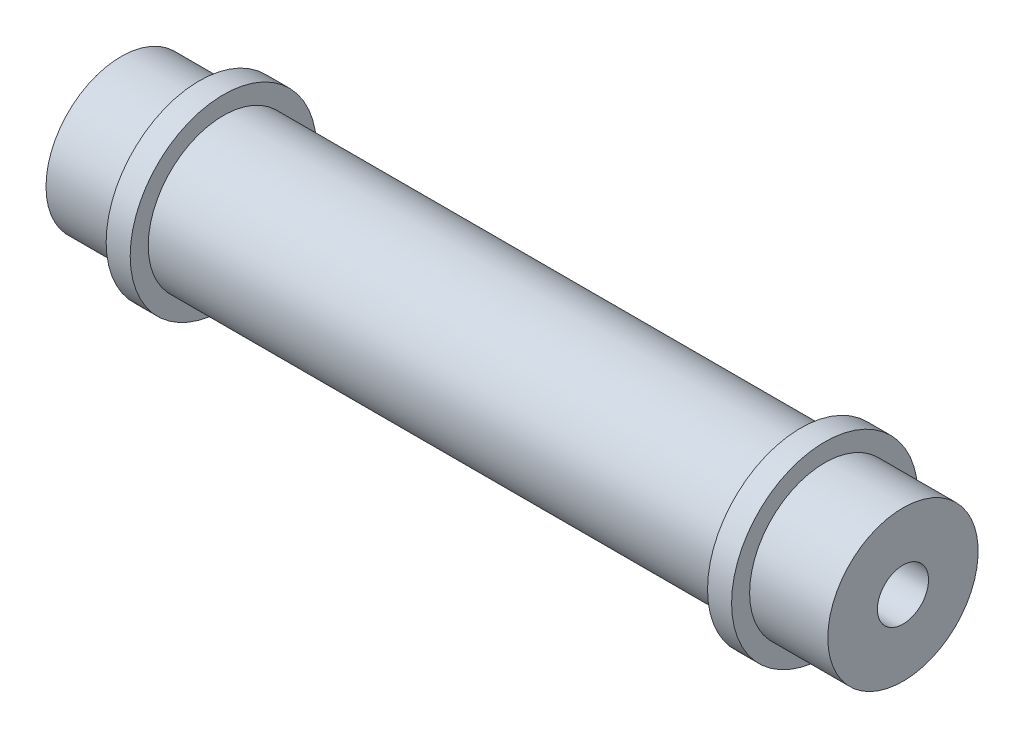
SolidWorks part; units mm, degrees
material "AISI 1020"
ref_plane "Спереди" through (0, 0, 0) normal (0, 0, 1) x (1, 0, 0)
ref_plane "Сверху" through (0, 0, 0) normal (0, 1, 0) x (1, 0, 0)
ref_plane "Справа" through (0, 0, 0) normal (1, 0, 0) x (0, 0, -1)
sketch "Эскиз1" plane through (0, 0, 0) normal (0, 0, 1) x (1, 0, 0)
  line L0 (-1000, 0) -> (49000, 0) construction
  line L1 (0, 0) -> (0, 12.5)
  line L4 (0, 12.5) -> (48, 12.5)
  line L5 (48, 12.5) -> (48, 15.5)
  line L6 (48, 15.5) -> (52, 15.5)
  line L7 (52, 15.5) -> (52, 12.5)
  line L8 (52, 12.5) -> (65, 12.5)
  line L9 (65, 12.5) -> (65, 0)
  line L10 (65, 0) -> (0, 0)
  line L11 (67, 12.5) -> (52, 12.5) construction
  line L12 (52, 12.5) -> (52, -12.5) construction
  line L13 (67, -12.5) -> (67, 12.5) construction
  dimension "D1" = 3
  dimension "4" = 4
  dimension "D4" = 2
revolve "Повернуть1" add sketch "Эскиз1" angle 360 about L0
hole_wizard "Отверстие обработанное метчиком M101" positions "Эскиз2" profile "Эскиз3" tap size "M10" standard "ISO"
sketch "Эскиз2" plane through (65, 0, 0) normal (1, 0, 0) x (0, 0, -1)
  point P0 (0, 0)
sketch "Эскиз3" plane through (65, 0, 0) normal (0, 1, 0) x (0, 0, -1)
  line L0 (0, 0) -> (0, 25.0537)
  line L1 (0, 25.0537) -> (4.25, 22.5)
  line L2 (4.25, 22.5) -> (4.25, 0)
  line L5 (4.25, 0) -> (0, 0)
  line L10 (0, 25.0537) -> (-4.25, 22.5) construction
  line L11 (0, -6.35) -> (0, 107.95) construction
  dimension "Диаметр сверла" = 8.5
  dimension "Глубина сверла" = 22.5
  dimension "Угол заточки сверла" = 118
cosmetic thread "Отверстие резьбы1" parameters "D1"=15, "D2"=10
mirror "Зеркальное отражение1" about plane through (0, 0, 0) normal (1, 0, 0) of bodies 104
